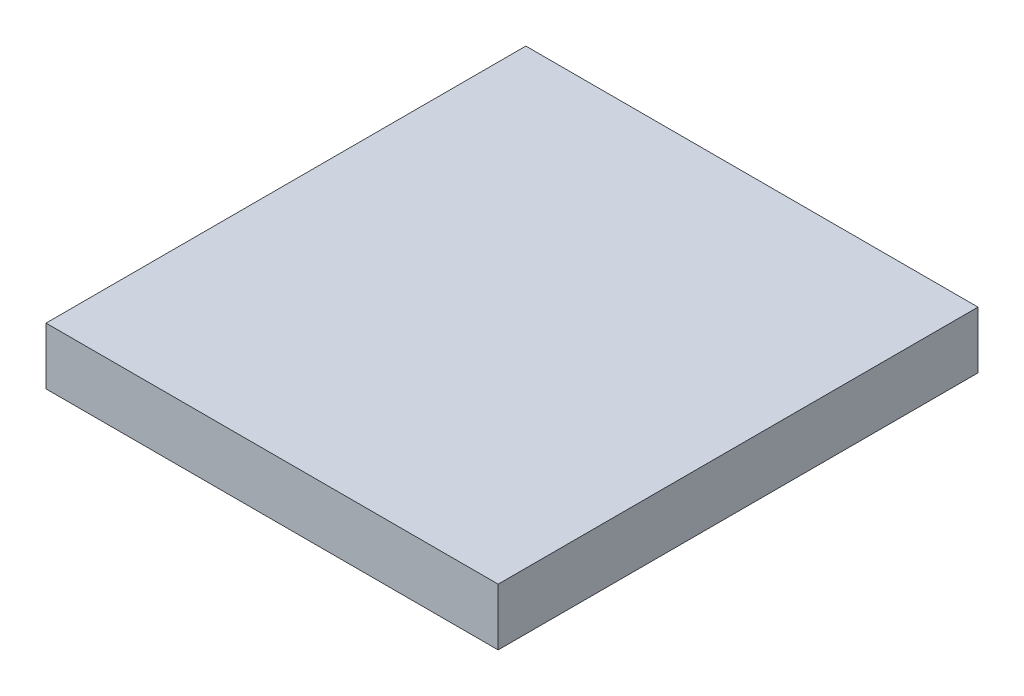
SolidWorks part; units mm, degrees
ref_plane "Спереди" through (0, 0, 0) normal (0, 0, 1) x (1, 0, 0)
ref_plane "Сверху" through (0, 0, 0) normal (0, 1, 0) x (1, 0, 0)
ref_plane "Справа" through (0, 0, 0) normal (1, 0, 0) x (0, 0, -1)
sketch "Эскиз1" plane through (0, 0, 0) normal (0, 1, 0) x (1, 0, 0)
  line L1 (0, 0) -> (238, 0)
  line L2 (0, 0) -> (0, 252.5805)
  line L3 (0, 252.5805) -> (238, 252.5805)
  line L4 (238, 0) -> (238, 252.5805)
  point P5 (0, 252.5805)
extrude "Бобышка-Вытянуть1" add sketch "Эскиз1" along normal blind 30
